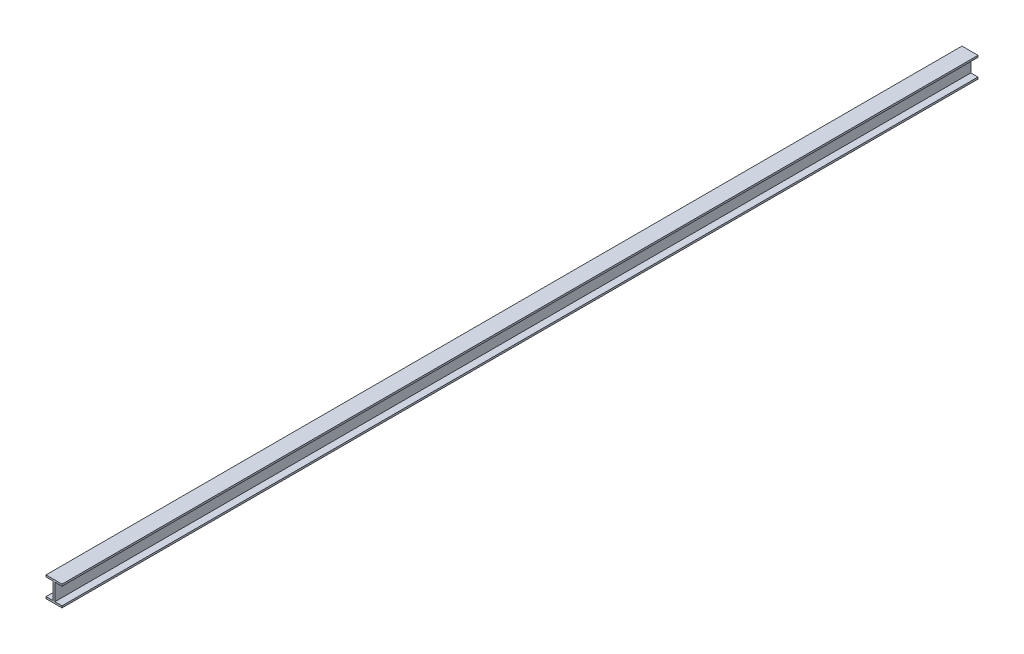
SolidWorks part; units mm, degrees
ref_plane "Front Plane" through (0, 0, 0) normal (0, 0, 1) x (1, 0, 0)
ref_plane "Top Plane" through (0, 0, 0) normal (0, 1, 0) x (1, 0, 0)
ref_plane "Right Plane" through (0, 0, 0) normal (1, 0, 0) x (0, 0, -1)
sketch "Sketch1" plane through (0, 0, 0) normal (0, 0, 1) x (1, 0, 0)
  line L0 (156, -32) -> (280, -32)
  line L1 (0, 0) -> (280, 0)
  line L2 (0, 0) -> (0, -32)
  line L3 (0, -360) -> (280, -360)
  line L4 (280, 0) -> (280, -32)
  line L5 (124, 0) -> (156, 0)
  line L6 (124, -32) -> (124, -328)
  line L7 (124, -360) -> (156, -360)
  line L8 (156, -32) -> (156, -328)
  line L9 (0, 0) -> (280, 0)
  line L10 (0, 0) -> (0, -32)
  line L11 (0, -32) -> (124, -32)
  line L12 (280, 0) -> (280, -32)
  line L13 (0, -360) -> (280, -360)
  line L14 (0, -360) -> (0, -328)
  line L15 (0, -328) -> (124, -328)
  line L16 (280, -360) -> (280, -328)
  line L17 (0, -328) -> (0, -360)
  line L18 (280, -328) -> (280, -360)
  line L19 (156, -328) -> (280, -328)
  dimension "D1" = 280
  dimension "D2" = 360
  dimension "D3" = 32
  dimension "D4" = 32
  dimension "D5" = 124
  dimension "D6" = 124
extrude "Boss-Extrude1" add sketch "Sketch1" along normal blind 16000 contours L19 L8 L0 L4 L1 L2 L11 L6 L15 L14 L3 L16
